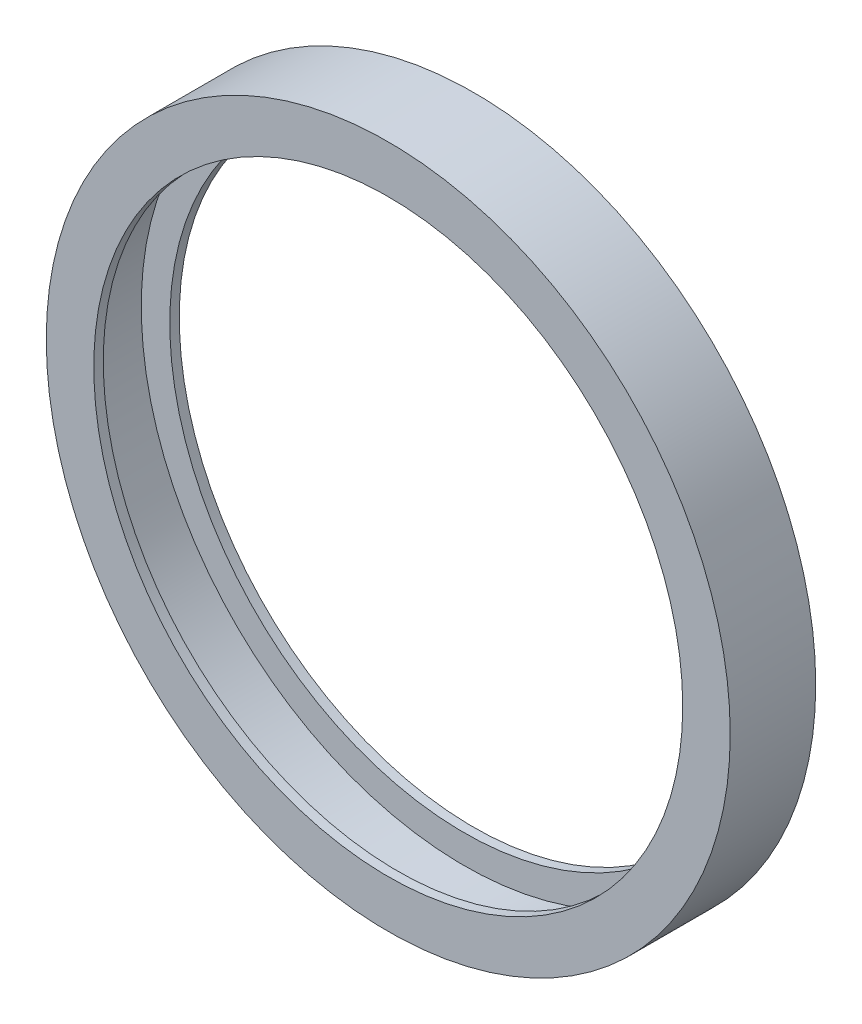
SolidWorks part; units mm, degrees
ref_plane "Front Plane" through (0, 0, 0) normal (0, 0, 1) x (1, 0, 0)
ref_plane "Top Plane" through (0, 0, 0) normal (0, 1, 0) x (1, 0, 0)
ref_plane "Right Plane" through (0, 0, 0) normal (1, 0, 0) x (0, 0, -1)
sketch "Sketch1" plane through (0, 0, 0) normal (0, 0, 1) x (1, 0, 0)
  circle A0 centre (0, 0) radius 36
  circle A1 centre (0, 0) radius 31
  dimension "D1" = 72
  dimension "D2" = 62
extrude "Boss-Extrude1" add sketch "Sketch1" along normal blind 1
sketch "Sketch2" plane through (0, 0, 1) normal (0, 0, 1) x (1, 0, 0)
  circle A0 centre (0, 0) radius 36 construction
  circle A1 centre (0, 0) radius 36
  circle A2 centre (0, 0) radius 34
  dimension "D1" = 2
extrude "Boss-Extrude2" add sketch "Sketch2" along normal blind 7
sketch "Sketch3" plane through (0, 0, 8) normal (0, 0, 1) x (1, 0, 0)
  circle A0 centre (0, 0) radius 36 construction
  circle A1 centre (0, 0) radius 36
  circle A2 centre (0, 0) radius 31 construction
  circle A3 centre (0, 0) radius 31
extrude "Boss-Extrude3" add sketch "Sketch3" along normal blind 1
